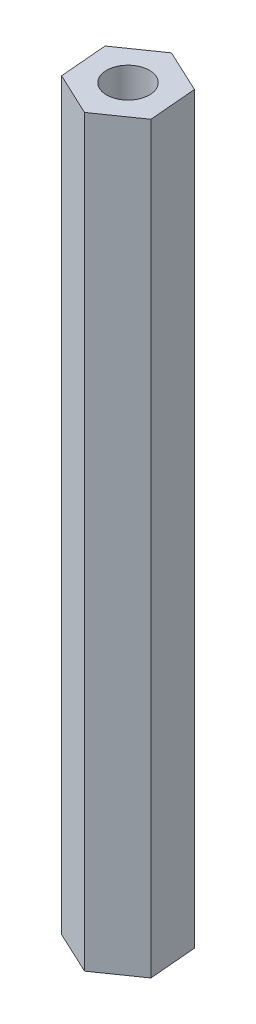
SolidWorks part; units mm, degrees
ref_plane "Front Plane" through (0, 0, 0) normal (0, 0, 1) x (1, 0, 0)
ref_plane "Top Plane" through (0, 0, 0) normal (0, 1, 0) x (1, 0, 0)
ref_plane "Right Plane" through (0, 0, 0) normal (1, 0, 0) x (0, 0, -1)
sketch "Sketch1" plane through (0, 0, 0) normal (0, 1, 0) x (1, 0, 0)
  line L1 (6.0165, 4.191) -> (-0.6213, 7.306)
  line L2 (-0.6213, 7.306) -> (-6.6378, 3.115)
  line L3 (-6.6378, 3.115) -> (-6.0165, -4.191)
  line L4 (-6.0165, -4.191) -> (0.6213, -7.306)
  line L5 (0.6213, -7.306) -> (6.6378, -3.115)
  line L6 (6.6378, -3.115) -> (6.0165, 4.191)
  circle A0 centre (0, 0) radius 6.35 construction
  dimension "D1" = 12.7
extrude "Boss-Extrude1" add sketch "Sketch1" along normal mid plane 114.3
sketch "Sketch2" plane through (0, 57.15, 0) normal (0, 1, 0) x (1, 0, 0)
  circle A0 centre (0, 0) radius 3.2893
  dimension "D1" = 6.5786
extrude "Cut-Extrude1" cut sketch "Sketch2" against normal blind 12.7
mirror "Mirror1" about plane through (0, 0, 0) normal (0, 1, 0) of "Cut-Extrude1"
